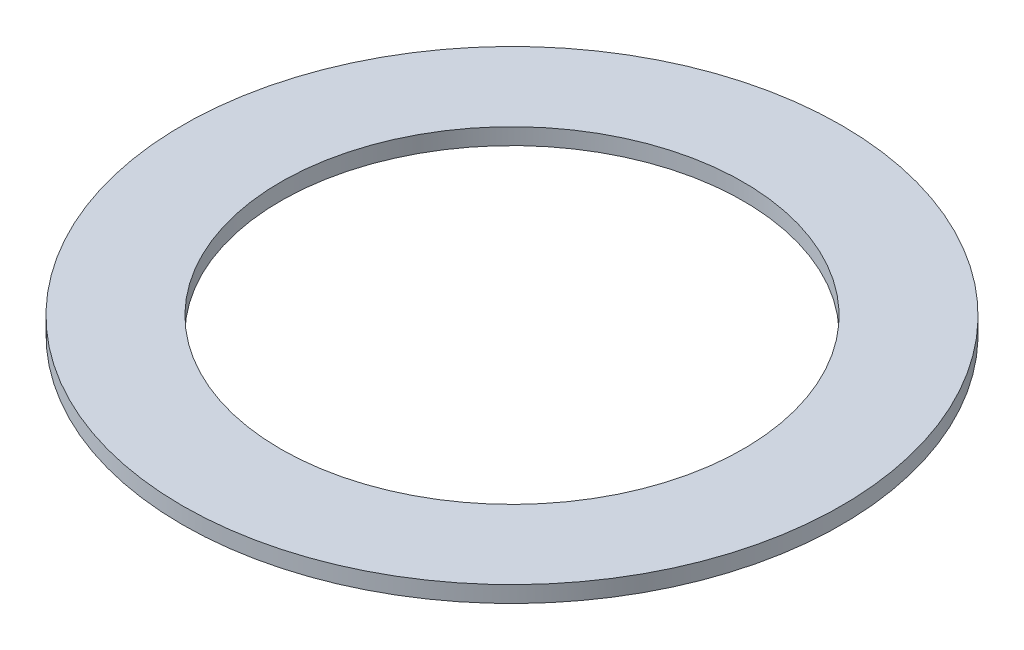
SolidWorks part; units mm, degrees
ref_plane "Front Plane" through (0, 0, 0) normal (0, 0, 1) x (1, 0, 0)
ref_plane "Top Plane" through (0, 0, 0) normal (0, 1, 0) x (1, 0, 0)
ref_plane "Right Plane" through (0, 0, 0) normal (1, 0, 0) x (0, 0, -1)
sketch "Sketch1" plane through (0, 0, 0) normal (0, 1, 0) x (1, 0, 0)
  circle A0 centre (0, 0) radius 70.625
  circle A1 centre (0, 0) radius 100.625
  dimension "D1" = 141.25
  dimension "D2" = 30
extrude "Boss-Extrude1" add sketch "Sketch1" along normal blind 5
